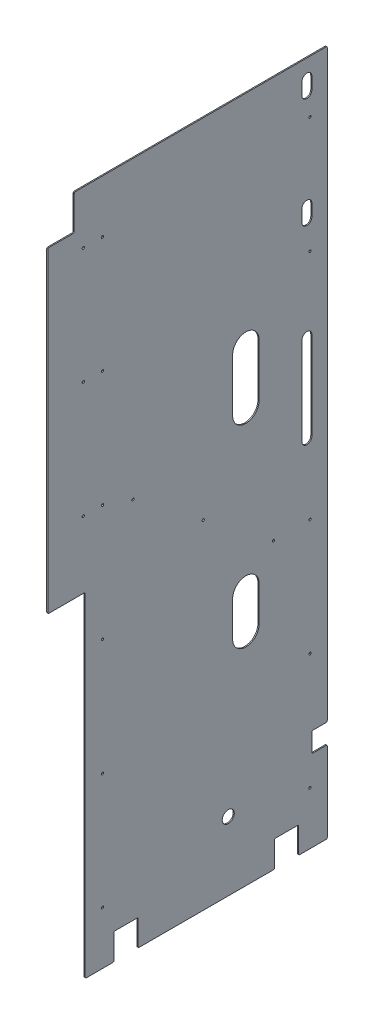
SolidWorks part; units mm, degrees
material "PC High Viscosity"
ref_plane "Front Plane" through (0, 0, 0) normal (0, 0, 1) x (1, 0, 0)
ref_plane "Top Plane" through (0, 0, 0) normal (0, 1, 0) x (1, 0, 0)
ref_plane "Right Plane" through (0, 0, 0) normal (1, 0, 0) x (0, 0, -1)
sketch "Sketch1" plane through (0, 0, 0) normal (1, 0, 0) x (0, 0, -1)
  line L1 (0, 0) -> (-806.45, 0)
  line L2 (0, 0) -> (0, 1981.2)
  line L3 (0, 1981.2) -> (-806.45, 1981.2)
  line L4 (-806.45, 0) -> (-806.45, 1981.2)
  dimension "D1" = 806.45
  dimension "D2" = 1981.2
extrude "Boss-Extrude1" add sketch "Sketch1" along normal blind 3.175
sketch "Sketch2" plane through (3.175, 0, 0) normal (1, 0, 0) x (0, 0, -1)
  line L0 (-806.45, 1981.2) -> (-806.45, 0) construction
  line L1 (-806.45, 0) -> (-762, 0) construction
  line L2 (-806.45, 0) -> (-806.45, 44.45) construction
  line L3 (-806.45, 44.45) -> (-762, 44.45) construction
  line L4 (-762, 0) -> (-762, 44.45) construction
  line L5 (-806.45, 933.45) -> (-762, 933.45) construction
  line L6 (-806.45, 933.45) -> (-806.45, 889) construction
  line L7 (-806.45, 889) -> (-762, 889) construction
  line L8 (-762, 933.45) -> (-762, 889) construction
  line L9 (-806.45, 965.2) -> (-698.5, 965.2)
  line L11 (-698.5, 965.2) -> (-698.5, 0)
  line L12 (-806.45, 0) -> (0, 0) construction
  line L13 (-698.5, 0) -> (-806.45, 0)
  line L14 (-806.45, 0) -> (-806.45, 965.2)
  line L21 (-806.45, 1981.2) -> (-730.25, 1981.2)
  line L22 (-806.45, 1981.2) -> (-806.45, 1879.6)
  line L23 (-806.45, 1879.6) -> (-730.25, 1879.6)
  line L24 (-730.25, 1981.2) -> (-730.25, 1879.6)
  point P21 (-762, 911.225)
  dimension "D1" = 44.45
  dimension "D2" = 889
  dimension "D3" = 965.2
  dimension "D4" = 107.95
  dimension "D6" = 76.2
  dimension "D7" = 101.6
extrude "Cut-Extrude1" cut sketch "Sketch2" against normal through all
hole_wizard "H (0.266) Diameter Hole1" positions "Sketch3" profile "Sketch4" hole size "H" standard "ANSI Inch" end condition through all
sketch "Sketch3" plane through (3.175, 0, 0) normal (1, 0, 0) x (0, 0, -1)
  line L0 (-698.5, 1981.2) -> (-698.5, 0) construction
  line L1 (0, 1981.2) -> (-730.25, 1981.2) construction
  line L2 (-698.5, 0) -> (0, 0) construction
  line L4 (0, 0) -> (0, 1981.2) construction
  line L5 (-654.05, 1981.2) -> (-654.05, 0) construction
  line L9 (-44.45, 0) -> (-44.45, 1981.2)
  line L10 (-44.45, 0) -> (-44.45, 1981.2) construction
  line L15 (-698.5, 44.45) -> (0, 44.45)
  line L16 (-698.5, 44.45) -> (0, 44.45) construction
  line L20 (0, 1936.75) -> (-730.25, 1936.75)
  line L21 (0, 1936.75) -> (-730.25, 1936.75) construction
  line L22 (-349.25, 44.45) -> (-349.25, 1936.75) construction
  line L23 (-654.05, 990.6) -> (-44.45, 990.6) construction
  line L25 (-654.05, 1981.2) -> (-698.5, 1981.2) construction
  line L27 (-676.275, 1981.2) -> (-676.275, 0) construction
  line L29 (-44.45, 1981.2) -> (0, 1981.2) construction
  line L31 (-22.225, 1981.2) -> (-22.225, 0) construction
  point P10 (-704.0562, 1828.8)
  point P12 (-648.4937, 1828.8)
  point P53 (-349.25, 990.6)
  point P92 (-704.0563, 1493.52)
  point P93 (-648.4938, 1493.52)
  point P94 (-704.0563, 1158.24)
  point P95 (-648.4938, 1158.24)
  point P97 (-648.4938, 822.96)
  point P99 (-648.4938, 487.68)
  point P101 (-648.4938, 152.4)
  point P104 (-50.0062, 152.4)
  point P105 (-50.0062, 487.68)
  point P106 (-50.0062, 822.96)
  point P107 (-50.0062, 1158.24)
  point P108 (-50.0062, 1493.52)
  point P109 (-50.0062, 1828.8)
  point P112 (-704.0563, 822.96)
  point P114 (-704.0563, 487.68)
  point P117 (-704.0562, 152.4)
  dimension "D1" = 698.5
  dimension "D6" = 55.5625
  dimension "D8" = 152.4
  dimension "D9" = 152.4
  dimension "D10" = 335.28
  dimension "D2" = 44.45
  dimension "D3" = 44.45
  dimension "D4" = 44.45
  dimension "D5" = 44.45
  dimension "D7" = 6
sketch "Sketch4" plane through (3.175, 1828.8, 50.0062) normal (0, 1, 0) x (0, 0, -1)
  line L0 (0, 0) -> (0, 3.175)
  line L1 (0, 3.175) -> (3.3782, 3.175)
  line L2 (3.3782, 3.175) -> (3.3782, 0)
  line L5 (3.3782, 0) -> (0, 0)
  line L11 (0, -6.35) -> (0, 107.95) construction
  dimension "Thru Hole Dia." = 6.7564
  dimension "Thru Hole Depth" = 3.175
sketch "Sketch5" plane through (3.175, 0, 0) normal (1, 0, 0) x (0, 0, -1)
  line L0 (-698.5, 0) -> (0, 0) construction
  line L1 (-82.55, 0) -> (-152.4, 0)
  line L2 (-82.55, 0) -> (-82.55, 76.2)
  line L3 (-82.55, 76.2) -> (-152.4, 76.2)
  line L4 (-152.4, 0) -> (-152.4, 76.2)
  line L5 (0, 0) -> (0, 1981.2) construction
  line L6 (-546.1, 0) -> (-615.95, 0)
  line L7 (-546.1, 0) -> (-546.1, 76.2)
  line L8 (-546.1, 76.2) -> (-615.95, 76.2)
  line L9 (-615.95, 0) -> (-615.95, 76.2)
  dimension "D1" = 82.55
  dimension "D2" = 546.1
  dimension "D3" = 69.85
  dimension "D4" = 76.2
extrude "Cut-Extrude2" cut sketch "Sketch5" against normal through all
fillet "Fillet1" radius 3.175 16 edges at (1.5875, 1981.2, 0) (1.5875, 0, 0) (1.5875, 0, 82.55) (1.5875, 76.2, 82.55) (1.5875, 76.2, 152.4) (1.5875, 0, 152.4) (1.5875, 76.2, 615.95) (1.5875, 0, 615.95) (1.5875, 0, 546.1) (1.5875, 76.2, 546.1) (1.5875, 0, 698.5) (1.5875, 965.2, 806.45) (1.5875, 965.2, 698.5) (1.5875, 1879.6, 806.45) (1.5875, 1879.6, 730.25) (1.5875, 1981.2, 730.25)
sketch "Sketch7" plane through (3.175, 0, 0) normal (1, 0, 0) x (0, 0, -1)
  line L5 (0, 3.175) -> (0, 1978.025) construction
  line L6 (-542.925, 0) -> (-155.575, 0) construction
  circle A0 centre (-285.75, 198.12) radius 17.399
  dimension "D3" = 34.798
  dimension "D1" = 285.75
  dimension "D2" = 198.12
extrude "Cut-Extrude4" cut sketch "Sketch7" against normal blind 6.35
sketch "Sketch8" plane through (3.175, 0, 0) normal (1, 0, 0) x (0, 0, -1)
  line L0 (0, 292.1) -> (-44.45, 292.1)
  line L1 (0, 292.1) -> (0, 234.95)
  line L2 (-44.45, 292.1) -> (-44.45, 234.95)
  line L3 (0, 234.95) -> (-44.45, 234.95)
  line L4 (0, 3.175) -> (0, 1978.025) construction
  line L5 (-79.375, 0) -> (-3.175, 0) construction
  dimension "D1" = 292.1
  dimension "D2" = 234.95
  dimension "D3" = 44.45
extrude "Cut-Extrude5" cut sketch "Sketch8" against normal through all
sketch "Sketch9" plane through (3.175, 0, 0) normal (1, 0, 0) x (0, 0, -1)
  line L0 (0, 733.425) -> (-806.45, 1341.1287) construction
  line L1 (0, 292.1) -> (0, 1978.025) construction
  line L2 (-806.45, 1876.425) -> (-806.45, 968.375) construction
  line L3 (-79.375, 0) -> (-3.175, 0) construction
  line L4 (-542.925, 0) -> (-155.575, 0) construction
  line L5 (-588.2749, 1176.7219) -> (-611.2041, 1146.2939) construction
  line L6 (-611.2041, 1146.2939) -> (-124.3559, 779.4275) construction
  line L7 (-124.3559, 779.4275) -> (-101.4267, 809.8555) construction
  line L8 (-561.0796, 1128.4001) -> (-155.3727, 822.678) construction
  circle A0 centre (-561.0796, 1128.4001) radius 3.3782
  circle A1 centre (-358.2262, 975.5391) radius 3.3782
  circle A2 centre (-155.3727, 822.678) radius 3.3782
  dimension "D6" = 22.225
  dimension "D10" = 6.7564
  dimension "D1" = 733.425
  dimension "D2" = 37
  dimension "D3" = 38.1
  dimension "D4" = 609.6
  dimension "D5" = 127
  dimension "D7" = 50.8
  dimension "D8" = 50.8
  dimension "D9" = 304.8
extrude "Cut-Extrude6" cut sketch "Sketch9" against normal through all
sketch "Sketch10" plane through (3.175, 0, 0) normal (1, 0, 0) x (0, 0, -1)
  line L0 (-58.7375, 1282.7) -> (-58.7375, 1028.7) construction
  line L1 (-44.45, 1282.7) -> (-44.45, 1028.7)
  line L2 (-73.025, 1282.7) -> (-73.025, 1028.7)
  line L3 (-58.7375, 1576.3875) -> (-58.7375, 1611.3125) construction
  line L4 (-73.025, 1576.3875) -> (-73.025, 1611.3125)
  line L5 (-44.45, 1576.3875) -> (-44.45, 1611.3125)
  line L6 (-58.7375, 1928.8125) -> (-58.7375, 1893.8875) construction
  line L7 (-44.45, 1928.8125) -> (-44.45, 1893.8875)
  line L8 (-73.025, 1928.8125) -> (-73.025, 1893.8875)
  line L18 (0, 292.1) -> (0, 1978.025) construction
  line L20 (-542.925, 0) -> (-155.575, 0) construction
  arc A0 (-44.45, 1282.7) -> (-73.025, 1282.7) centre (-58.7375, 1282.7) ccw
  arc A1 (-73.025, 1028.7) -> (-44.45, 1028.7) centre (-58.7375, 1028.7) ccw
  arc A2 (-73.025, 1576.3875) -> (-44.45, 1576.3875) centre (-58.7375, 1576.3875) ccw
  arc A3 (-44.45, 1611.3125) -> (-73.025, 1611.3125) centre (-58.7375, 1611.3125) ccw
  arc A4 (-44.45, 1928.8125) -> (-73.025, 1928.8125) centre (-58.7375, 1928.8125) ccw
  arc A5 (-73.025, 1893.8875) -> (-44.45, 1893.8875) centre (-58.7375, 1893.8875) ccw
  point P2 (-58.7375, 1155.7)
  point P7 (-58.7375, 1593.85)
  point P14 (-58.7375, 1911.35)
  dimension "D1" = 34.925
  dimension "D2" = 34.925
  dimension "D3" = 28.575
  dimension "D6" = 254
  dimension "D7" = 44.45
  dimension "D12" = 1155.7
  dimension "D13" = 1593.85
  dimension "D14" = 1911.35
extrude "Cut-Extrude7" cut sketch "Sketch10" against normal through all
sketch "Sketch11" plane through (3.175, 0, 0) normal (1, 0, 0) x (0, 0, -1)
  line L0 (-234.95, 736.6) -> (-234.95, 635) construction
  line L1 (-196.85, 736.6) -> (-196.85, 635)
  line L2 (-273.05, 736.6) -> (-273.05, 635)
  line L3 (-234.95, 1346.2) -> (-234.95, 1193.8) construction
  line L4 (-196.85, 1346.2) -> (-196.85, 1193.8)
  line L5 (-273.05, 1346.2) -> (-273.05, 1193.8)
  line L6 (-806.45, 1876.425) -> (-806.45, 968.375) construction
  line L7 (-803.275, 1879.6) -> (-733.425, 1879.6) construction
  arc A0 (-196.85, 736.6) -> (-273.05, 736.6) centre (-234.95, 736.6) ccw
  arc A1 (-273.05, 635) -> (-196.85, 635) centre (-234.95, 635) ccw
  arc A2 (-196.85, 1346.2) -> (-273.05, 1346.2) centre (-234.95, 1346.2) ccw
  arc A3 (-273.05, 1193.8) -> (-196.85, 1193.8) centre (-234.95, 1193.8) ccw
  point P2 (-234.95, 685.8)
  point P7 (-234.95, 1270)
  point P16 (-196.85, 685.8)
  dimension "D1" = 571.5
  dimension "D2" = 76.2
  dimension "D3" = 101.6
  dimension "D4" = 152.4
  dimension "D5" = 609.6
  dimension "D6" = 1193.8
extrude "Cut-Extrude8" cut sketch "Sketch11" against normal through all
fillet "Fillet2" radius 3.175 4 edges at (1.5875, 234.95, 44.45) (1.5875, 234.95, 0) (1.5875, 292.1, 44.45) (1.5875, 292.1, 0)
